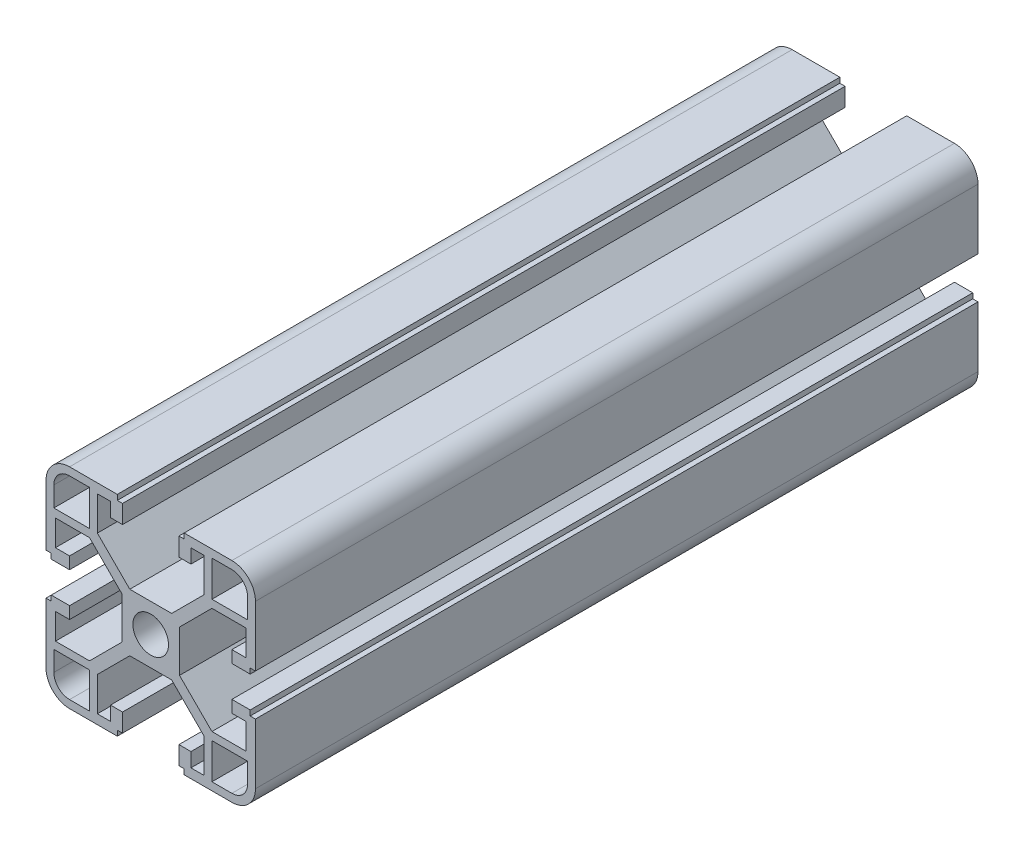
SolidWorks part; units mm, degrees
material "6061-T6 (SS)"
ref_plane "Front Plane" through (0, 0, 0) normal (0, 0, 1) x (1, 0, 0)
ref_plane "Top Plane" through (0, 0, 0) normal (0, 1, 0) x (1, 0, 0)
ref_plane "Right Plane" through (0, 0, 0) normal (1, 0, 0) x (0, 0, -1)
sketch "Sketch1" plane through (0, 0, 0) normal (0, 0, 1) x (1, 0, 0)
  line L0 (3.4, 0) -> (5.5, 0)
  line L1 (10.19, 11.69) -> (4, 5.5)
  line L2 (11.69, 10.19) -> (5.5, 4)
  line L3 (18.2, 10.19) -> (11.69, 10.19)
  line L4 (18.2, 10.19) -> (18.2, 5.2656)
  line L5 (18.2, 5.2656) -> (15.5, 5.2656)
  line L6 (15.5, 5.2656) -> (15.5, 2.9656)
  line L7 (15.5, 2.9656) -> (19, 2.9656)
  line L8 (19, 2.9656) -> (19, 3.9656)
  line L9 (19, 3.9656) -> (20, 3.9656)
  line L10 (20, 3.9656) -> (20, 15.5)
  line L11 (15.5, 20) -> (6.3853, 20)
  line L12 (18.5, 11.69) -> (18.5, 15.5)
  line L13 (15.5, 18.5) -> (11.69, 18.5)
  line L14 (11.69, 11.69) -> (11.69, 18.5)
  line L15 (0, 3.4) -> (0, 5.5)
  line L16 (4, 5.5) -> (0, 5.5)
  line L17 (6.3853, 20) -> (6.3853, 19)
  line L18 (5.5, 0) -> (5.5, 4)
  line L19 (6.3853, 19) -> (5.3853, 19)
  line L20 (5.3853, 19) -> (5.3853, 15.5)
  line L21 (5.3853, 15.5) -> (7.6853, 15.5)
  line L22 (10.19, 11.69) -> (10.19, 18.2)
  line L23 (11.69, 11.69) -> (18.5, 11.69)
  line L24 (7.6853, 18.2) -> (7.6853, 15.5)
  line L25 (10.19, 18.2) -> (7.6853, 18.2)
  arc A0 (20, 15.5) -> (15.5, 20) centre (15.5, 15.5) ccw
  arc A1 (18.5, 15.5) -> (15.5, 18.5) centre (15.5, 15.5) ccw
  arc A2 (3.4, 0) -> (0, 3.4) centre (0, 0) ccw
  dimension "D3" = 4.5
  dimension "D18" = 1.5
  dimension "D9" = 3.4
  dimension "D20" = 1.8
  dimension "D25" = 3
  dimension "D1" = 5.5
  dimension "D2" = 1.5
  dimension "D4" = 14.5
  dimension "D5" = 1.5
  dimension "D6" = 2.1
  dimension "D7" = 2.3
  dimension "D8" = 1.8
  dimension "D10" = 6.81
  dimension "D11" = 2.1
  dimension "D12" = 1
  dimension "D13" = 4.5
  dimension "D14" = 45
  dimension "D15" = 14.5
  dimension "D16" = 1
  dimension "D17" = 1.5
  dimension "D19" = 6.81
  dimension "D21" = 4.5
  dimension "D22" = 2.3
  dimension "D23" = 1
  dimension "D24" = 1
  dimension "D26" = 8.754
  dimension "D27" = 8.754
  dimension "D28" = 4.9244
  dimension "D29" = 2.5047
extrude "Boss-Extrude1" add sketch "Sketch1" along normal blind 138
mirror "Mirror1" about plane through (0, 0, 0) normal (0, 1, 0) of "Boss-Extrude1"
mirror "Mirror2" about plane through (0, 0, 0) normal (1, 0, 0) of "Boss-Extrude1"
mirror "Mirror3" about plane through (0, 0, 0) normal (0, 1, 0) of "Mirror2"
